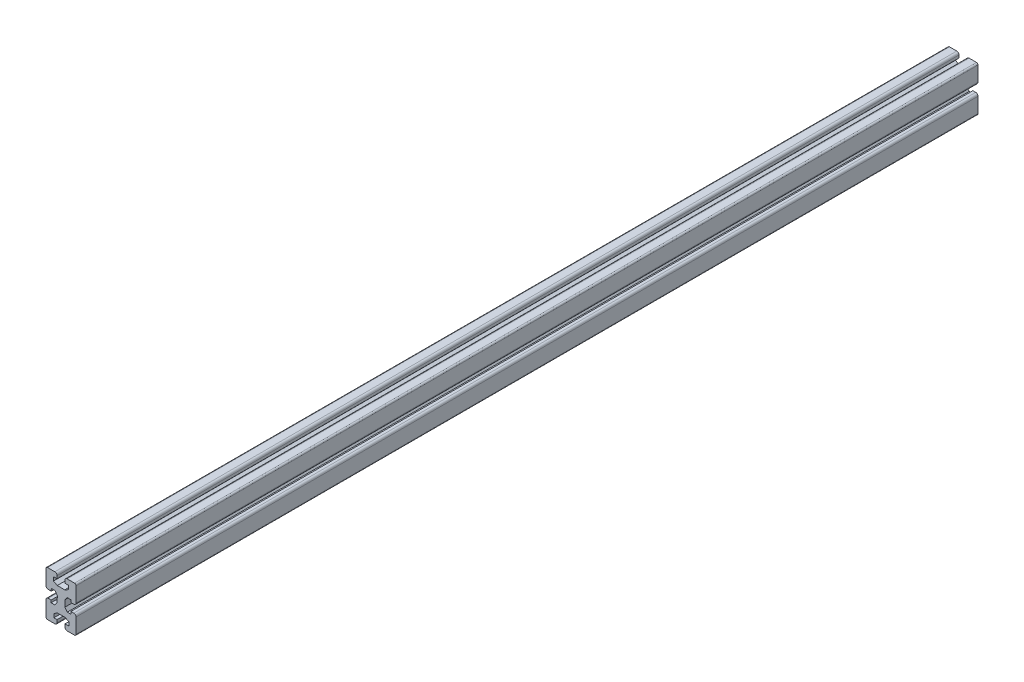
SolidWorks part; units mm, degrees
ref_plane "Alzado" through (0, 0, 0) normal (0, 0, 1) x (1, 0, 0)
ref_plane "Planta" through (0, 0, 0) normal (0, 1, 0) x (1, 0, 0)
ref_plane "Vista lateral" through (0, 0, 0) normal (1, 0, 0) x (0, 0, -1)
sketch "Croquis1" plane through (0, 0, 0) normal (0, 0, 1) x (1, 0, 0)
  line L0 (0, 0) -> (-20, 0) construction
  line L1 (20, -30) -> (5.2, -30)
  line L2 (20, -30) -> (20, -5)
  line L3 (20, 30) -> (5.2, 30)
  line L4 (-20, -30) -> (-20, -5)
  line L5 (20, -30) -> (-20, 30) construction
  line L6 (20, 30) -> (-20, -30) construction
  line L7 (-5.2, -5) -> (5.2, -5)
  line L8 (-5.2, -5) -> (-5.2, 5)
  line L9 (-5.2, 5) -> (5.2, 5)
  line L10 (5.2, -5) -> (5.2, 5)
  line L11 (-5.2, -5) -> (5.2, 5) construction
  line L12 (-5.2, 5) -> (5.2, -5) construction
  line L14 (10, -5) -> (10, 5.215)
  line L16 (-10, -5) -> (-10, 5.215)
  line L17 (10, -10) -> (-10, 10) construction
  line L18 (10, 10) -> (-10, -10) construction
  line L19 (0, 0) -> (0, 10) construction
  line L20 (-10, 5.215) -> (-20, 5.215)
  line L21 (-10, -5) -> (-20, -5)
  line L22 (10, -5) -> (20, -5)
  line L23 (20, 5.215) -> (10, 5.215)
  line L24 (-5.2, 20) -> (-5.2, 30)
  line L25 (5.2, 20) -> (5.2, 30)
  line L26 (5.2, -20) -> (5.2, -30)
  line L27 (-5.2, -20) -> (-5.2, -30)
  line L28 (20, 5.215) -> (20, 30)
  line L29 (-5.2, -30) -> (-20, -30)
  line L30 (-5.2, 30) -> (-20, 30)
  line L32 (-20, 5.215) -> (-20, 30)
  line L33 (-5.2, -30) -> (5.2, -30) construction
  line L34 (0, -30) -> (0, -20) construction
  line L36 (-5.2, -20) -> (5.2, -20)
  line L37 (-5.2, 20) -> (5.2, 20)
  point P0 (0, 0)
  point P6 (0, 0)
  point P11 (0, 0)
  dimension "D1" = 40
  dimension "D2" = 60
  dimension "D3" = 10
  dimension "D4" = 5.2
  dimension "D5" = 20
  dimension "D6" = 20
  dimension "D7" = 10
extrude "Saliente-Extruir1" add sketch "Croquis1" along normal blind 1200 contours L26 L1 L2 L22 L14 L23 L28 L3 L25 L37 L24 L30 L32 L20 L16 L21 L4 L29 L27 L36
fillet "Redondeo3" radius 2 4 edges at (-20, -30, 600) (20, -30, 600) (20, 30, 600) (-20, 30, 600)
fillet "Redondeo4" radius 3 8 edges at (5.2, 30, 600) (20, -5, 600) (20, 5.215, 600) (-5.2, 30, 600) (-20, -5, 600) (-20, 5.215, 600) (5.2, -30, 600) (-5.2, -30, 600)
sketch "Croquis2" plane through (0, 0, 1200) normal (0, 0, 1) x (1, 0, 0)
  line L0 (0, 0) -> (0, 20) construction
  line L1 (-5.2, 20) -> (5.2, 20) construction
  line L2 (0, 20) -> (0, 23.452) construction
  line L3 (-10, 23.452) -> (10, 23.452)
  line L4 (10, 23.452) -> (10, 18.452)
  line L5 (10, 18.452) -> (5, 15.7561)
  line L6 (5, 15.7561) -> (-5, 15.7561)
  line L7 (-10, 18.452) -> (-5, 15.7561)
  line L8 (-10, 23.452) -> (-10, 18.452)
  line L9 (0, 0) -> (10, 0.1075) construction
  line L10 (10, -5) -> (10, 5.215) construction
  line L11 (-9.601, -18.6627) -> (-4.6601, -15.8599)
  line L12 (-9.4935, -23.6616) -> (-9.601, -18.6627)
  line L13 (-9.4935, -23.6616) -> (10.5018, -23.2316)
  line L14 (10.5018, -23.2316) -> (10.3944, -18.2328)
  line L15 (10.3944, -18.2328) -> (5.3376, -15.6449)
  line L16 (5.3376, -15.6449) -> (-4.6601, -15.8599)
  line L17 (10, 0.1075) -> (13, 0.1075) construction
  line L18 (13, 0.1075) -> (13, 0.1397)
  line L19 (13, 8.4777) -> (8.1055, 8.4777)
  line L20 (8.1055, 8.4777) -> (5, 4.2926)
  line L22 (8.2859, -8.3015) -> (5.0911, -4.1841)
  line L23 (12.9993, 0.172) -> (13, 0.1397)
  line L24 (13.1792, -8.1962) -> (8.2859, -8.3015)
  line L26 (13, 8.4777) -> (13.1792, -8.1962)
  line L27 (5, 4.2926) -> (5.0911, -4.1841)
  line L28 (-13, 8.4777) -> (-8.1055, 8.4777)
  line L29 (-13, 8.4777) -> (-13.1792, -8.1962)
  line L30 (-13.1792, -8.1962) -> (-8.2859, -8.3015)
  line L31 (-8.2859, -8.3015) -> (-5.0911, -4.1841)
  line L32 (-5, 4.2926) -> (-5.0911, -4.1841)
  line L33 (-8.1055, 8.4777) -> (-5, 4.2926)
  point P11 (0, 15.7561)
  dimension "D1" = 5
  dimension "D2" = 10
  dimension "D3" = 20
  dimension "D4" = 8.4767
extrude "Cortar-Extruir1" cut sketch "Croquis2" against normal blind 1200
sketch "Croquis3" plane through (5.0456, 0.0542, 0) normal (0.9999, 0.0107, 0) x (0, 0, -1)
  line L0 (-1200, 0) -> (-1182, 0) construction
  line L1 (-1200, 4.2386) -> (-1200, -4.2386) construction
  line L2 (-600, 4.2386) -> (-600, -4.2386) construction
  line L3 (0, 4.2386) -> (-1200, 4.2386) construction
  line L4 (0, -4.2386) -> (-1200, -4.2386) construction
  circle A0 centre (-1182, 0) radius 3
  circle A1 centre (-18, 0) radius 3
  dimension "D1" = 18
extrude "Cortar-Extruir2" cut sketch "Croquis3" against normal blind 96 and the other way blind 56
